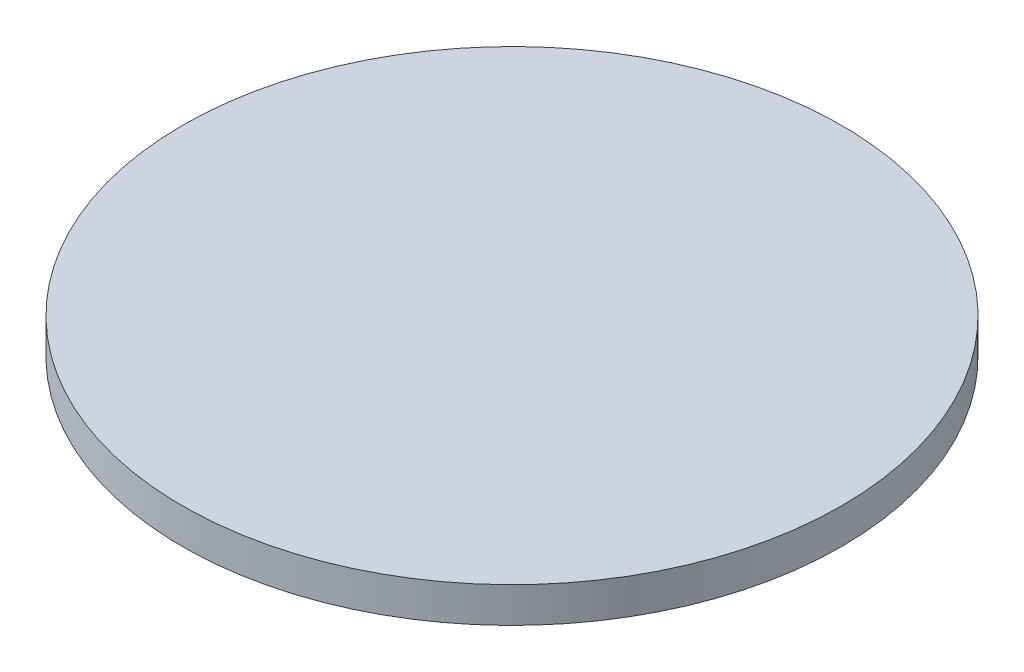
SolidWorks part; units mm, degrees
material "ABS"
ref_plane "Front Plane" through (0, 0, 0) normal (0, 0, 1) x (1, 0, 0)
ref_plane "Top Plane" through (0, 0, 0) normal (0, 1, 0) x (1, 0, 0)
ref_plane "Right Plane" through (0, 0, 0) normal (1, 0, 0) x (0, 0, -1)
sketch "Sketch1" plane through (0, 0, 0) normal (0, 0, 1) x (1, 0, 0)
  line L0 (0, 0) -> (-36.5125, 0)
  line L1 (-36.5125, 0) -> (-38.1, -1.5875)
  line L2 (-38.1, -1.5875) -> (-44.45, -1.5875)
  line L3 (-44.45, -1.5875) -> (-44.45, 3.175)
  line L4 (-44.45, 3.175) -> (0, 3.175)
  line L5 (0, 3.175) -> (0, 0)
  point P3 (-38.7127, 0)
  dimension "D1" = 44.45
  dimension "D2" = 4.7625
  dimension "D3" = 45
  dimension "D4" = 3.175
  dimension "D5" = 6.35
revolve "Revolve1" add sketch "Sketch1" angle 360 about L5
